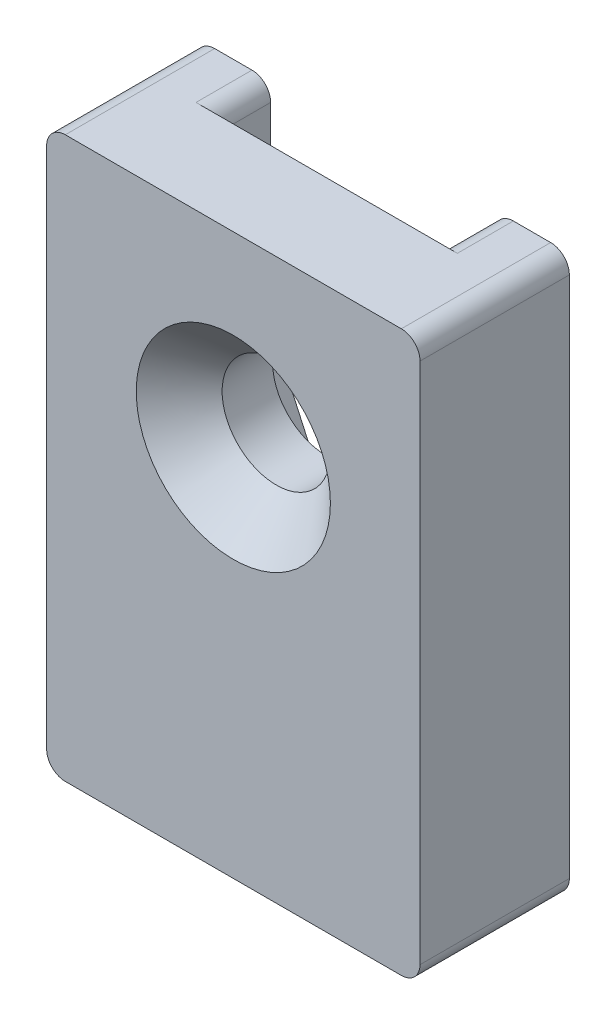
SolidWorks part; units mm, degrees
ref_plane "Front Plane" through (0, 0, 0) normal (0, 0, 1) x (1, 0, 0)
ref_plane "Top Plane" through (0, 0, 0) normal (0, 1, 0) x (1, 0, 0)
ref_plane "Right Plane" through (0, 0, 0) normal (1, 0, 0) x (0, 0, -1)
sketch "Sketch2" plane through (0, 0, 0) normal (0, 0, 1) x (1, 0, 0)
  line L1 (-6, -15) -> (6, -15)
  line L2 (-6, -15) -> (-6, 15)
  line L3 (-6, 15) -> (6, 15)
  line L4 (6, -15) -> (6, 15)
  line L5 (-6, -15) -> (6, 15) construction
  line L6 (-6, 15) -> (6, -15) construction
  point P0 (0, 0)
  dimension "D1" = 12
  dimension "D2" = 30
sketch "Sketch3" plane through (0, 0, 0) normal (0, 0, 1) x (1, 0, 0)
  line L0 (-6, 15) -> (6, 15) construction
  line L1 (-10, 15) -> (10, 15)
  line L2 (-10, 15) -> (-10, -15)
  line L3 (-10, -15) -> (10, -15)
  line L4 (10, 15) -> (10, -15)
  line L5 (-6, -15) -> (6, -15) construction
  point P8 (0, -15)
  point P9 (0, -15)
  dimension "D1" = 20
extrude "Boss-Extrude1" add sketch "Sketch3" against normal mid plane 8
sketch "Sketch4" plane through (0, 0, -4) normal (0, 0, -1) x (-1, 0, 0)
  line L1 (-6, 15) -> (6, 15)
  line L2 (-6, 15) -> (-6, -15)
  line L3 (-6, -15) -> (6, -15)
  line L4 (6, 15) -> (6, -15)
extrude "Cut-Extrude1" cut sketch "Sketch4" against normal blind 3
sketch "Sketch5" plane through (0, 0, 4) normal (0, 0, 1) x (1, 0, 0)
  line L0 (0, 15) -> (0, 5) construction
  line L1 (-6, 15) -> (6, 15) construction
  dimension "D1" = 10
hole_wizard "CSK for M5 Flat Head Machine Screw1" positions "3DSketch1" profile "Sketch6" countersink size "M5" standard "ANSI Metric" end condition through all
sketch3d "3DSketch1"
  point P0 (0, 5, 4)
sketch "Sketch6" plane through (0, 5, 4) normal (1, 0, 0) x (0, -1, 0)
  line L0 (0, 0) -> (0, 8)
  line L1 (0, 8) -> (2.9, 8)
  line L2 (2.9, 8) -> (2.9, 2.3)
  line L3 (2.9, 2.3) -> (5.2, 0)
  line L5 (5.2, 0) -> (0, 0)
  line L6 (-2.9, 2.3) -> (-5.2, 0) construction
  line L11 (0, -6.35) -> (0, 107.95) construction
  dimension "Thru Hole Dia." = 5.8
  dimension "Thru Hole Depth" = 8
  dimension "Near C'Sink Dia." = 10.4
  dimension "Near C'Sink Angle" = 90
sketch "Sketch7" plane through (0, 0, -1) normal (0, 0, -1) x (-1, 0, 0)
  line L0 (6, -15) -> (6, 15) construction
  line L1 (5.4622, 2.5172) -> (-2.5, -15)
  line L2 (6, -15) -> (-6, -15) construction
  line L3 (-2.5, -15) -> (6, -15)
  line L4 (6, -15) -> (6, 5)
  arc A0 (6, 5) -> (5.4622, 2.5172) centre (0, 5) cw
  circle A1 centre (0, 5) radius 2.9 construction
  point P7 (0, 0)
  dimension "D1" = 3.5
extrude "Boss-Extrude2" add sketch "Sketch7" along normal up to surface (3 mm away) up to face at (-8, 0, -4)
fillet "Fillet1" radius 1 8 edges at (-10, 15, 0) (10, 15, 0) (10, -15, 0) (-10, -15, 0) (6, 15, -2.5) (-6, 15, -2.5) (2.5, -15, -2.5) (6, -15, -2.5)
sketch "Sketch1" plane through (0, 0, 0) normal (0, 1, 0) x (1, 0, 0)
  line L1 (-73.5224, -88.5584) -> (73.5224, -88.5584)
  line L2 (-73.5224, -88.5584) -> (-73.5224, 88.5584)
  line L3 (-73.5224, 88.5584) -> (73.5224, 88.5584)
  line L4 (73.5224, -88.5584) -> (73.5224, 88.5584)
  line L5 (-73.5224, -88.5584) -> (73.5224, 88.5584) construction
  line L6 (-73.5224, 88.5584) -> (73.5224, -88.5584) construction
  point P0 (0, 0)
